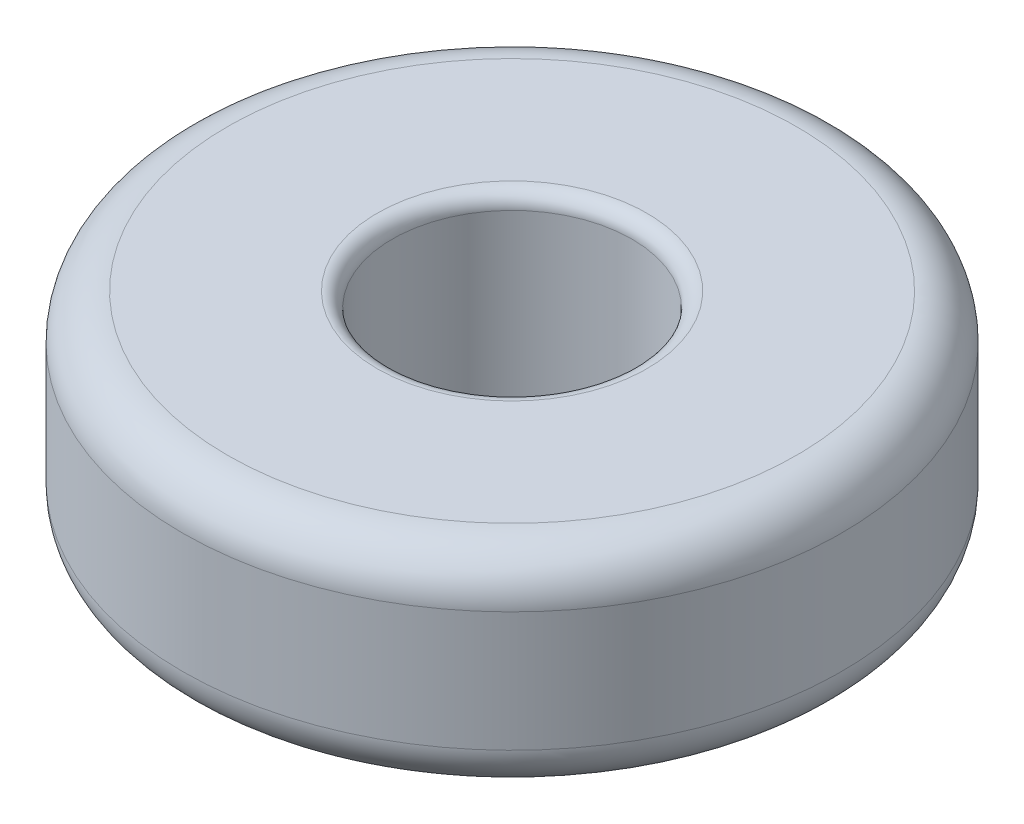
SolidWorks part; units mm, degrees
material "Red plastic appearance"
ref_plane "Front Plane" through (0, 0, 0) normal (0, 0, 1) x (1, 0, 0)
ref_plane "Top Plane" through (0, 0, 0) normal (0, 1, 0) x (1, 0, 0)
ref_plane "Right Plane" through (0, 0, 0) normal (1, 0, 0) x (0, 0, -1)
sketch "Sketch1" plane through (0, 0, 0) normal (0, 1, 0) x (1, 0, 0)
  circle A0 centre (0, 0) radius 4
  circle A1 centre (0, 0) radius 11
  dimension "D1" = 8
  dimension "D2" = 22
extrude "Boss-Extrude1" add sketch "Sketch1" along normal mid plane 7
fillet "Fillet1" radius 1.5 2 edges at (0, -3.5, 11) (0, 3.5, 11)
fillet "Fillet2" radius 0.5 2 edges at (0, -3.5, 4) (0, 3.5, 4)
